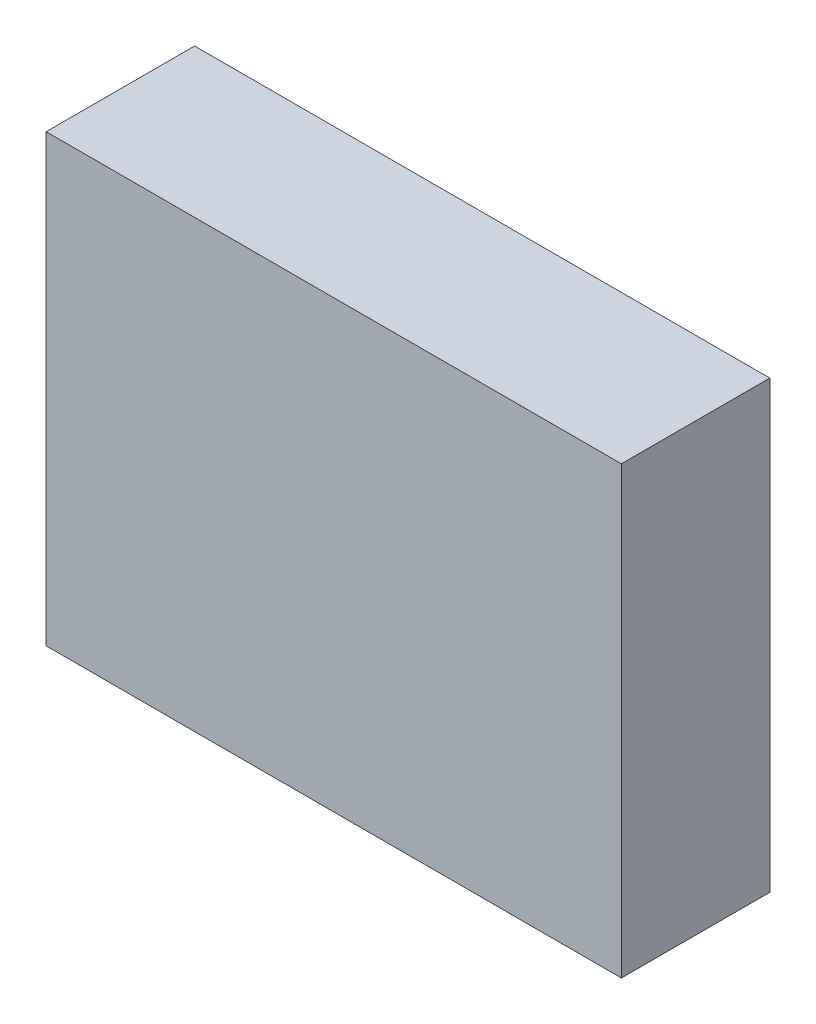
SolidWorks part; units mm, degrees
ref_plane "Front Plane" through (0, 0, 0) normal (0, 0, 1) x (1, 0, 0)
ref_plane "Top Plane" through (0, 0, 0) normal (0, 1, 0) x (1, 0, 0)
ref_plane "Right Plane" through (0, 0, 0) normal (1, 0, 0) x (0, 0, -1)
sketch "Sketch1" plane through (0, 0, 0) normal (0, 0, 1) x (1, 0, 0)
  line L1 (-98.425, -76.2) -> (98.425, -76.2)
  line L2 (-98.425, -76.2) -> (-98.425, 76.2)
  line L3 (-98.425, 76.2) -> (98.425, 76.2)
  line L4 (98.425, -76.2) -> (98.425, 76.2)
  line L5 (-98.425, -76.2) -> (98.425, 76.2) construction
  line L6 (-98.425, 76.2) -> (98.425, -76.2) construction
  point P0 (0, 0)
  dimension "D1" = 152.4
  dimension "D2" = 196.85
extrude "Boss-Extrude1" add sketch "Sketch1" along normal blind 50.8
